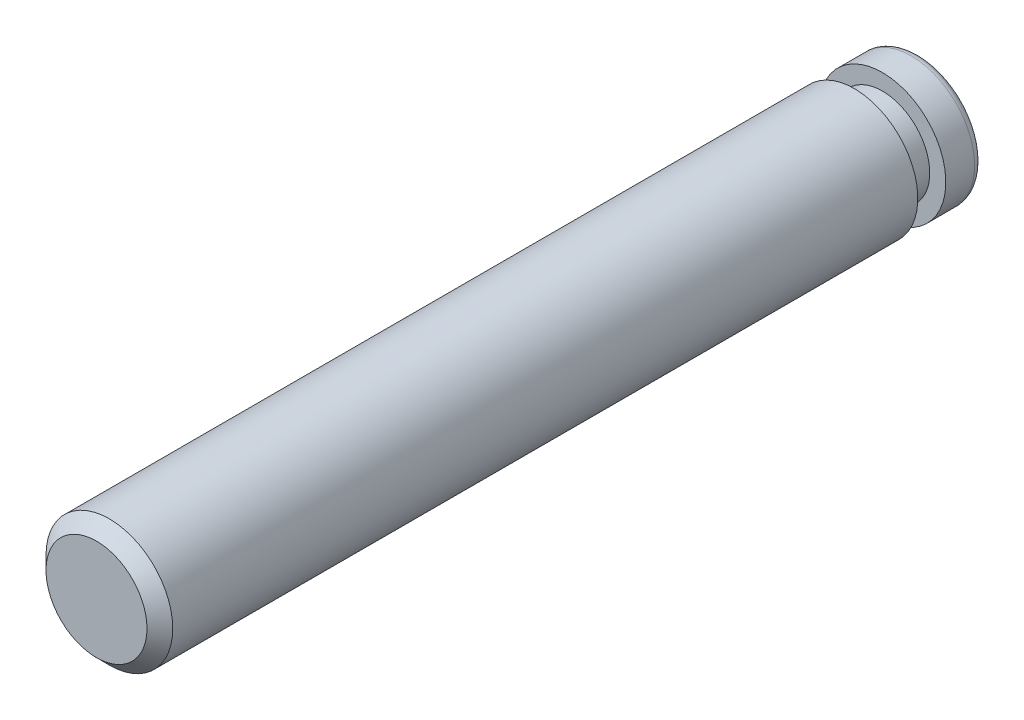
SolidWorks part; units mm, degrees
material "AISI 304"
ref_plane "Front Plane" through (0, 0, 0) normal (0, 0, 1) x (1, 0, 0)
ref_plane "Top Plane" through (0, 0, 0) normal (0, 1, 0) x (1, 0, 0)
ref_plane "Right Plane" through (0, 0, 0) normal (1, 0, 0) x (0, 0, -1)
sketch "Sketch1" plane through (0, 0, 0) normal (0, 0, 1) x (1, 0, 0)
  circle A0 centre (0, 0) radius 1.9558
  dimension "D1" = 3.9116
extrude "Extrude1" add sketch "Sketch1" along normal mid plane 25.4
sketch "Sketch2" plane through (0, 0, 0) normal (0, 1, 0) x (1, 0, 0)
  line L0 (0, 10.0425) -> (0, -1.1158) construction
  line L1 (1.9558, -12.7) -> (1.9558, 12.7) construction
  line L2 (1.4605, 11.557) -> (1.9558, 11.557)
  line L3 (1.4605, 11.557) -> (1.4605, 10.6934)
  line L4 (1.4605, 10.6934) -> (1.9558, 10.6934)
  line L5 (1.9558, 11.557) -> (1.9558, 10.6934)
  line L6 (-1.9558, -12.7) -> (1.9558, -12.7) construction
  dimension "D1" = 1.4605
  dimension "D2" = 23.3934
  dimension "D3" = 0.8636
revolve "Cut-Revolve1" cut sketch "Sketch2" angle 360 about L0
fillet "Fillet1" radius 0.254 1 edges at (1.9558, 0, -12.7)
chamfer "Chamfer1" distance 0.3969 angle 45 1 edges at (1.9558, 0, 12.7)
